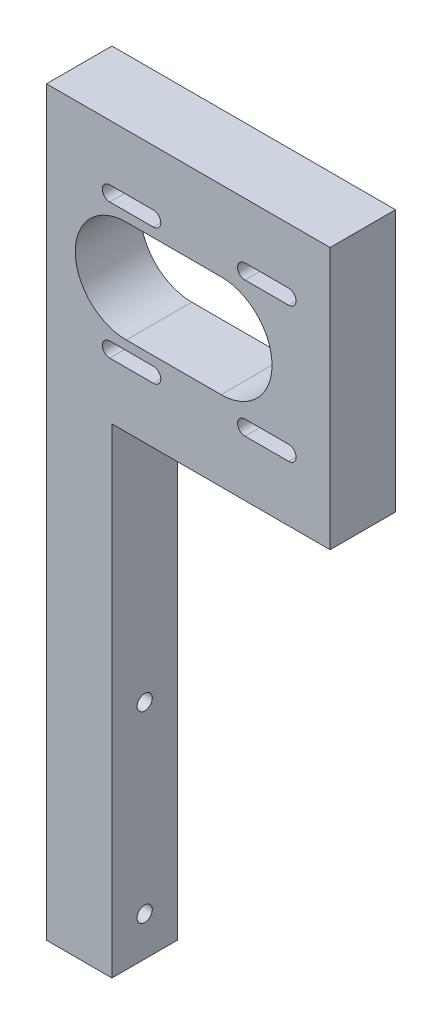
SolidWorks part; units mm, degrees
ref_plane "Front Plane" through (0, 0, 0) normal (0, 0, 1) x (1, 0, 0)
ref_plane "Top Plane" through (0, 0, 0) normal (0, 1, 0) x (1, 0, 0)
ref_plane "Right Plane" through (0, 0, 0) normal (1, 0, 0) x (0, 0, -1)
sketch "Sketch1" plane through (0, 0, 0) normal (0, 1, 0) x (1, 0, 0)
  line L1 (7.5, 7.5) -> (-7.5, 7.5)
  line L2 (7.5, 7.5) -> (7.5, -7.5)
  line L3 (7.5, -7.5) -> (-7.5, -7.5)
  line L4 (-7.5, 7.5) -> (-7.5, -7.5)
  point P4 (7.5, 0)
  point P6 (0, 7.5)
  dimension "D1" = 15
  dimension "D2" = 15
extrude "Boss-Extrude1" add sketch "Sketch1" along normal blind 170
sketch "Sketch2" plane through (7.5, 0, 0) normal (1, 0, 0) x (0, 0, -1)
  line L0 (-7.5, 0) -> (7.5, 0) construction
  circle A0 centre (0, 9) radius 1.75
  circle A1 centre (0, 51) radius 1.75
  dimension "D1" = 9
  dimension "D2" = 42
extrude "Cut-Extrude1" cut sketch "Sketch2" against normal through all
sketch "Sketch8" plane through (7.5, 0, 0) normal (1, 0, 0) x (0, 0, -1)
  line L0 (7.5, 170) -> (7.5, 0) construction
  line L1 (-7.5, 170) -> (7.5, 170)
  line L2 (-7.5, 170) -> (-7.5, 110)
  line L3 (-7.5, 110) -> (7.5, 110)
  line L4 (7.5, 170) -> (7.5, 110)
  dimension "D1" = 60
extrude "Boss-Extrude2" add sketch "Sketch8" along normal blind 50
sketch "Sketch9" plane through (57.5, 0, 0) normal (1, 0, 0) x (0, 0, -1)
  line L0 (-7.5, 170) -> (-7.5, 110) construction
  line L1 (-7.5, 161) -> (7.5, 161)
  line L2 (-7.5, 161) -> (-7.5, 139)
  line L3 (-7.5, 139) -> (7.5, 139)
  line L4 (7.5, 161) -> (7.5, 139)
  line L5 (7.5, 110) -> (7.5, 170) construction
  line L6 (7.5, 170) -> (-7.5, 170) construction
  dimension "D1" = 22
  dimension "D2" = 9
extrude "Cut-Extrude2" cut sketch "Sketch9" against normal blind 31
sketch "Sketch11" plane through (-7.5, 0, 0) normal (-1, 0, 0) x (0, 0, 1)
  line L0 (-7.5, 170) -> (7.5, 170) construction
  circle A0 centre (0, 161) radius 4.05
  circle A1 centre (0, 119) radius 4.05
  dimension "D1" = 9
  dimension "D2" = 42
extrude "Cut-Extrude3" cut sketch "Sketch11" against normal blind 10
sketch "Sketch12" plane through (26.5, 0, 0) normal (1, 0, 0) x (0, 0, -1)
  line L1 (-7.5, 161) -> (7.5, 161)
  line L2 (-7.5, 161) -> (-7.5, 139)
  line L3 (-7.5, 139) -> (7.5, 139)
  line L4 (7.5, 161) -> (7.5, 139)
extrude "Boss-Extrude3" add sketch "Sketch12" along normal blind 31
sketch "Sketch13" plane through (0, 0, 7.5) normal (0, 0, 1) x (1, 0, 0)
  line L0 (17, 124.5) -> (7, 124.5) construction
  line L1 (17, 122.8) -> (7, 122.8)
  line L2 (32.5, 140) -> (10.8, 140) construction
  line L3 (32.5, 128.3) -> (10.8, 128.3)
  line L4 (32.5, 151.7) -> (10.8, 151.7)
  line L5 (17, 126.2) -> (7, 126.2)
  line L6 (48, 124.5) -> (38, 124.5) construction
  line L7 (48, 122.8) -> (38, 122.8)
  line L8 (48, 126.2) -> (38, 126.2)
  line L9 (48, 155.5) -> (38, 155.5) construction
  line L10 (48, 153.8) -> (38, 153.8)
  line L11 (48, 157.2) -> (38, 157.2)
  line L12 (17, 155.5) -> (7, 155.5) construction
  line L13 (17, 153.8) -> (7, 153.8)
  line L14 (17, 157.2) -> (7, 157.2)
  line L15 (57.5, 170) -> (57.5, 110) construction
  arc A0 (17, 122.8) -> (17, 126.2) centre (17, 124.5) ccw
  arc A1 (32.5, 128.3) -> (32.5, 151.7) centre (32.5, 140) ccw
  arc A2 (10.8, 151.7) -> (10.8, 128.3) centre (10.8, 140) ccw
  arc A3 (7, 126.2) -> (7, 122.8) centre (7, 124.5) ccw
  arc A4 (48, 122.8) -> (48, 126.2) centre (48, 124.5) ccw
  arc A5 (38, 126.2) -> (38, 122.8) centre (38, 124.5) ccw
  arc A6 (48, 153.8) -> (48, 157.2) centre (48, 155.5) ccw
  arc A7 (38, 157.2) -> (38, 153.8) centre (38, 155.5) ccw
  arc A8 (17, 153.8) -> (17, 157.2) centre (17, 155.5) ccw
  arc A9 (7, 157.2) -> (7, 153.8) centre (7, 155.5) ccw
  point P3 (12, 124.5)
  point P6 (21.65, 140)
  point P16 (43, 124.5)
  point P23 (43, 155.5)
  point P30 (12, 155.5)
  dimension "D1" = 15.5
  dimension "D2" = 25
  dimension "D3" = 15.5
  dimension "D4" = 15.5
  dimension "D5" = 15.5
  dimension "D6" = 15.5
  dimension "D7" = 15.5
extrude "Cut-Extrude4" cut sketch "Sketch13" against normal through all
